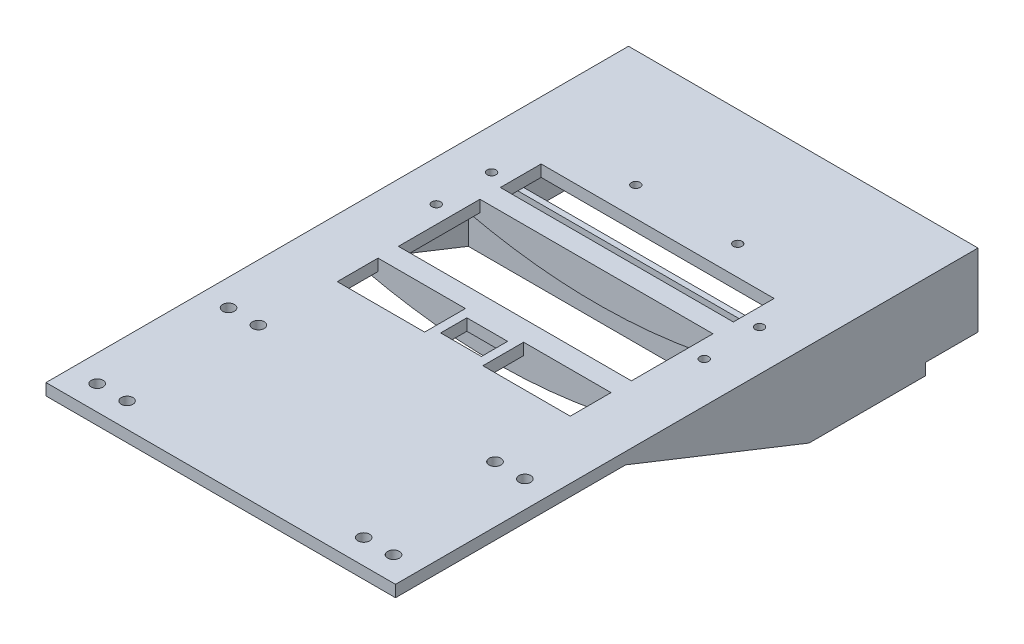
SolidWorks part; units mm, degrees
ref_plane "Front Plane" through (0, 0, 0) normal (0, 0, 1) x (1, 0, 0)
ref_plane "Top Plane" through (0, 0, 0) normal (0, 1, 0) x (1, 0, 0)
ref_plane "Right Plane" through (0, 0, 0) normal (1, 0, 0) x (0, 0, -1)
sketch "Sketch1" plane through (0, 0, 0) normal (0, 1, 0) x (1, 0, 0)
  line L0 (0, 0) -> (0, 199.1037) construction
  line L1 (-60, -40) -> (60, -40)
  line L2 (-60, -40) -> (-60, 40)
  line L3 (-40, 40) -> (40, 40)
  line L4 (60, -40) -> (60, 40)
  line L5 (-60, -40) -> (0, 0) construction
  line L6 (-60, 40) -> (60, -40) construction
  line L7 (17.5, 120) -> (-17.5, 120) construction
  line L8 (-60, 40) -> (-60, 160)
  line L9 (-40, 110) -> (40, 110)
  line L10 (60, 160) -> (60, 40)
  line L11 (-40, 40) -> (-40, 110)
  line L12 (40, 40) -> (40, 110)
  line L13 (-60, 160) -> (60, 160)
  circle A0 centre (-17.5, 120) radius 1.5
  circle A1 centre (17.5, 120) radius 1.5
  circle A2 centre (-50.87, -31.55) radius 2.025
  circle A3 centre (-40.62, -31.55) radius 2.01
  circle A4 centre (-50.87, 13.55) radius 2.025
  circle A5 centre (-40.62, 13.55) radius 2.025
  circle A6 centre (40.62, 13.55) radius 2.025
  circle A7 centre (50.87, 13.55) radius 2.025
  circle A8 centre (50.87, -31.55) radius 2.025
  circle A9 centre (40.62, -31.55) radius 2.01
  point P0 (0, 0)
  point P11 (0, 120)
  dimension "D5" = 3
  dimension "D6" = 3
  dimension "D10" = 10
  dimension "D12" = 4.05
  dimension "D13" = 8.45
  dimension "D14" = 9.13
  dimension "D15" = 4.02
  dimension "D16" = 8.45
  dimension "D17" = 19.38
  dimension "D18" = 9.13
  dimension "D19" = 19.38
  dimension "D20" = 53.55
  dimension "D21" = 53.55
  dimension "D22" = 200
  dimension "D1" = 80
  dimension "D2" = 120
  dimension "D3" = 35
  dimension "D4" = 160
  dimension "D7" = 20
  dimension "D8" = 20
  dimension "D9" = 80
  dimension "D11" = 50
extrude "Boss-Extrude1" add sketch "Sketch1" along normal blind 4
sketch "Sketch2" plane through (0, 0, 0) normal (0, -1, 0) x (1, 0, 0)
  line L0 (0, -160) -> (0, -25.4341) construction
  line L1 (60, -160) -> (37, -160)
  line L2 (60, -160) -> (60, -142)
  line L3 (60, -142) -> (37, -142)
  line L4 (37, -160) -> (37, -142)
  line L5 (60, -160) -> (-60, -160) construction
  line L6 (-60, -160) -> (-60, -142)
  line L7 (-60, -142) -> (-37, -142)
  line L8 (-37, -160) -> (-37, -142)
  line L9 (-37, -160) -> (-60, -160)
  dimension "D1" = 23
  dimension "D2" = 18
extrude "Boss-Extrude2" add sketch "Sketch2" along normal blind 21
sketch "Sketch3" plane through (60, 0, 0) normal (1, 0, 0) x (0, 0, -1)
  line L1 (142, -21) -> (142, 4)
  line L2 (-40, 4) -> (160, 4) construction
  line L3 (142, 4) -> (39.0327, 4)
  line L4 (39.0327, 4) -> (39.0327, 0)
  line L5 (-40, 0) -> (142, 0) construction
  line L7 (142, -21) -> (142, -25)
  line L9 (142, -25) -> (102, -25)
  line L10 (39.0327, 0) -> (102, -25)
  dimension "D1" = 4
  dimension "D2" = 40
extrude "Boss-Extrude3" add sketch "Sketch3" against normal blind 3
mirror "Mirror1" about plane through (0, 0, 0) normal (1, 0, 0) of "Boss-Extrude3"
fillet "Fillet2" radius 5 2 edges at (-37, 0, -151) (37, 0, -151)
sketch "Sketch4" plane through (0, 4, 0) normal (0, 1, 0) x (1, 0, 0)
  line L0 (-40, 75) -> (40, 75) construction
  line L1 (-40, 110) -> (-40, 40) construction
  line L2 (40, 40) -> (40, 110) construction
  line L3 (-40, 96) -> (-40, 92.5)
  line L4 (40, 110) -> (-40, 110) construction
  line L5 (40, 92.5) -> (40, 89)
  line L6 (-40, 96) -> (40, 96)
  line L7 (40, 96) -> (40, 89)
  line L8 (40, 89) -> (-40, 89)
  line L9 (-40, 89) -> (-40, 96)
  line L10 (40, 54) -> (40, 61)
  line L11 (40, 57.5) -> (40, 61)
  line L12 (-40, 61) -> (-40, 54)
  line L13 (-40, 54) -> (-40, 57.5)
  line L14 (-40, 54) -> (40, 54)
  line L15 (40, 61) -> (-40, 61)
  line M16 (-40, 40) -> (-40, 110)
  line M18 (40, 110) -> (40, 40)
  dimension "D1" = 14
  dimension "D2" = 7
  dimension "D3" = 14
extrude "Boss-Extrude4" add sketch "Sketch4" against normal up to surface (4 mm away) contours L8 L6 M18 M16 | L15 L12 L14 L10 M18 M16 up to face at (40.62, 0, 29.54)
sketch "Sketch5" plane through (0, 0, -54) normal (0, 0, 1) x (1, 0, 0)
  line L0 (51.5501, 0) -> (-51.5501, 0)
  spline S0 degree 2 poles (51.5501, 0) (0, -14) (-51.5501, 0) knots 0 0 0 1 1 1
  point P3 (0, 0)
  dimension "D1" = 7
extrude "Boss-Extrude5" add sketch "Sketch5" against normal up to surface (35 mm away)
ref_plane "Plane1" through (0, 0, -75) normal (0, 0, 1) x (1, 0, 0)
mirror "Mirror3" about plane through (0, 0, -75) normal (0, 0, 1) of "Boss-Extrude5"
sketch "Sketch6" plane through (0, 0, 0) normal (0, 1, 0) x (1, 0, 0)
  line L4 (-40, 89) -> (-40, 61)
  line L5 (-40, 61) -> (40, 61)
  line L6 (40, 61) -> (40, 89)
  line L7 (40, 89) -> (-40, 89)
  line L8 (-40, 89) -> (-40, 61)
  line L9 (-40, 61) -> (40, 61)
  line L10 (40, 61) -> (40, 89)
  line L11 (40, 89) -> (-40, 89)
  dimension "D1" = 0
extrude "Cut-Extrude1" cut sketch "Sketch6" against normal blind 37
sketch "Sketch7" plane through (0, 4, 0) normal (0, 1, 0) x (1, 0, 0)
  line L0 (0, 0) -> (0, 179.3192) construction
  line L1 (10, 40) -> (-10, 40)
  line L2 (-40, 40) -> (40, 40) construction
  line L3 (-10, 40) -> (-10, 54)
  line L4 (-40, 54) -> (40, 54) construction
  line L5 (-10, 54) -> (10, 54)
  line L6 (10, 40) -> (10, 54)
  line L7 (7, 51.5) -> (-7, 51.5)
  line L8 (-7, 51.5) -> (-7, 42.5)
  line L9 (-7, 42.5) -> (7, 42.5)
  line L10 (7, 51.5) -> (7, 42.5)
  point P12 (0, 54)
  point P13 (0, 40)
  point P18 (0, 51.5)
  point P19 (0, 42.5)
  dimension "D1" = 20
  dimension "D2" = 14
  dimension "D3" = 2.5
  dimension "D4" = 9
extrude "Boss-Extrude6" add sketch "Sketch7" against normal up to surface (4 mm away)
sketch "Sketch8" plane through (40, 0, 0) normal (-1, 0, 0) x (0, 0, 1)
  line L0 (-89, -2.7854) -> (-89, 4) construction
  line L1 (-89, 0) -> (-61, 0)
  line L2 (-89, 0) -> (-89, -2.7854)
  line L3 (-89, -2.7854) -> (-61, -2.7854)
  line L4 (-61, 0) -> (-61, -2.7854)
  line L5 (-89, -2.7854) -> (-61, -2.7854) construction
  line L6 (-61, 4) -> (-89, 4) construction
  line L8 (-61, -2.7854) -> (-61, 4) construction
  dimension "D1" = 4
extrude "Cut-Extrude2" cut sketch "Sketch8" against normal up to vertex and the other way up to vertex
sketch "Sketch9" plane through (0, 4, 0) normal (0, 1, 0) x (1, 0, 0)
  line L0 (-40, 110) -> (-40, 96) construction
  line L1 (-40, 89) -> (-40, 61) construction
  line L2 (40, 110) -> (-40, 110) construction
  circle A0 centre (-46, 99) radius 1.5
  circle A1 centre (-46, 80) radius 1.5
  dimension "D1" = 3
  dimension "D2" = 3
  dimension "D3" = 6
  dimension "D4" = 6
  dimension "D5" = 30
  dimension "D6" = 11
extrude "Cut-Extrude3" cut sketch "Sketch9" against normal blind 40
mirror "Mirror4" about plane through (0, 0, 0) normal (1, 0, 0) of "Cut-Extrude3"
sketch "Sketch10" plane through (0, 0, 0) normal (0, -1, 0) x (1, 0, 0)
  circle A0 centre (-30.47, -12.29) radius 2.01
  circle A1 centre (-20.32, -12.29) radius 2.01
  circle A4 centre (-30.47, 31.55) radius 2.01
  circle A5 centre (-20.32, 31.55) radius 2.01
  circle A6 centre (-10.17, 31.55) radius 2.01
  circle A8 centre (10.13, 31.55) radius 2.01
  circle A9 centre (20.28, 31.55) radius 2.01
  circle A10 centre (30.43, 31.55) radius 2.01
  circle A11 centre (-30.47, 20.27) radius 2.01
  circle A12 centre (-20.32, 20.27) radius 2.01
  circle A13 centre (-10.17, 20.27) radius 2.01
  circle A15 centre (10.13, 20.27) radius 2.01
  circle A16 centre (20.28, 20.27) radius 2.01
  circle A17 centre (30.43, 20.27) radius 2.01
  circle A18 centre (-30.47, 8.99) radius 2.01
  circle A19 centre (-20.32, 8.99) radius 2.01
  circle A20 centre (-10.17, 8.99) radius 2.01
  circle A22 centre (10.13, 8.99) radius 2.01
  circle A23 centre (20.28, 8.99) radius 2.01
  circle A24 centre (30.43, 8.99) radius 2.01
  circle A25 centre (-30.47, -2.29) radius 2.01
  circle A26 centre (-20.32, -2.29) radius 2.01
  circle A27 centre (-10.17, -2.29) radius 2.01
  circle A29 centre (10.13, -2.29) radius 2.01
  circle A30 centre (20.28, -2.29) radius 2.01
  circle A31 centre (30.43, -2.29) radius 2.01
  circle A32 centre (-10.17, -12.29) radius 2.01
  circle A34 centre (10.13, -12.29) radius 2.01
  circle A35 centre (20.28, -12.29) radius 2.01
  circle A36 centre (30.43, -12.29) radius 2.01
  circle A37 centre (-30.47, -22.29) radius 2.01
  circle A38 centre (-20.32, -22.29) radius 2.01
  circle A39 centre (-10.17, -22.29) radius 2.01
  circle A41 centre (10.13, -22.29) radius 2.01
  circle A42 centre (20.28, -22.29) radius 2.01
  circle A43 centre (30.43, -22.29) radius 2.01
  circle A44 centre (-30.47, -32.29) radius 2.01
  circle A45 centre (-20.32, -32.29) radius 2.01
  circle A46 centre (-10.17, -32.29) radius 2.01
  circle A48 centre (10.13, -32.29) radius 2.01
  circle A49 centre (20.28, -32.29) radius 2.01
  circle A50 centre (30.43, -32.29) radius 2.01
  dimension "D2" = 4.02
  dimension "D1" = 4
extrude "Cut-Extrude4" cut sketch "Sketch10" against normal blind 40
sketch "Sketch11" plane through (0, 4, 0) normal (0, 1, 0) x (1, 0, 0)
  line L1 (-33.7485, 36.7107) -> (35.422, 36.7107)
  line L2 (-33.7485, 36.7107) -> (-33.7485, -36.3646)
  line L3 (-33.7485, -36.3646) -> (35.422, -36.3646)
  line L4 (35.422, 36.7107) -> (35.422, -36.3646)
extrude "Boss-Extrude7" add sketch "Sketch11" against normal blind 2
sketch "Sketch12" plane through (0, 0, 0) normal (1, 0, 0) x (0, 0, -1)
  line L2 (-40, 0) -> (39.0327, 0)
  spline S0 degree 2 poles (-40, 0) (-0.4684, -10.0015) (39.0327, 0) knots 0 0 0 1 1 1
  dimension "D1" = 5
extrude "Boss-Extrude8" add sketch "Sketch12" along normal mid plane 2
sketch "Sketch14" plane through (0, -21, 0) normal (0, -1, 0) x (1, 0, 0)
  line L0 (-60, -142) -> (-60, -160) construction
  circle A0 centre (-58, -144) radius 1
  circle A1 centre (-53.5, -144) radius 1
  circle A2 centre (-49, -144) radius 1
  circle A3 centre (-44.5, -144) radius 1
  circle A4 centre (-40, -144) radius 1
  circle A5 centre (-53.5, -148.5) radius 1
  circle A6 centre (-49, -148.5) radius 1
  circle A7 centre (-44.5, -148.5) radius 1
  circle A8 centre (-40, -148.5) radius 1
  circle A9 centre (-53.5, -153) radius 1
  circle A10 centre (-49, -153) radius 1
  circle A11 centre (-44.5, -153) radius 1
  circle A12 centre (-40, -153) radius 1
  circle A13 centre (-53.5, -157.5) radius 1
  circle A14 centre (-49, -157.5) radius 1
  circle A15 centre (-44.5, -157.5) radius 1
  circle A16 centre (-40, -157.5) radius 1
  circle A17 centre (-58, -148.5) radius 1
  circle A18 centre (-58, -153) radius 1
  circle A19 centre (-58, -157.5) radius 1
  dimension "D1" = 2
  dimension "D2" = 2
  dimension "D4" = 5
  dimension "D5" = 4
extrude "Cut-Extrude5" cut sketch "Sketch14" against normal up to surface (21 mm away)
mirror "Mirror5" about plane through (0, 0, 0) normal (1, 0, 0) of "Cut-Extrude5"
sketch "Sketch15" plane through (0, 0, 0) normal (0, -1, 0) x (1, 0, 0)
  line L0 (-22.5, -150) -> (22.5, -150) construction
  line L1 (-22.5, -145) -> (22.5, -145)
  line L2 (-22.5, -155) -> (22.5, -155)
  line L3 (32, -160) -> (-32, -160) construction
  line L4 (-22.5, -132) -> (22.5, -132) construction
  line L5 (-22.5, -127) -> (22.5, -127)
  line L6 (-22.5, -137) -> (22.5, -137)
  arc A0 (-22.5, -145) -> (-22.5, -155) centre (-22.5, -150) ccw
  arc A1 (22.5, -155) -> (22.5, -145) centre (22.5, -150) ccw
  arc A2 (-22.5, -127) -> (-22.5, -137) centre (-22.5, -132) ccw
  arc A3 (22.5, -137) -> (22.5, -127) centre (22.5, -132) ccw
  point P2 (0, -150)
  point P14 (0, -132)
  dimension "D2" = 5
  dimension "D1" = 5
  dimension "D3" = 45
  dimension "D5" = 8
  dimension "D4" = 2
extrude "Cut-Extrude6" cut sketch "Sketch15" against normal blind 2
sketch "Sketch16" plane through (0, 0, 0) normal (0, -1, 0) x (1, 0, 0)
  line L0 (-47, 20) -> (-47, -2) construction
  line L1 (-42, 20) -> (-42, -2)
  line L2 (-52, 20) -> (-52, -2)
  line L3 (-60, -39.0327) -> (-60, 40) construction
  line L4 (-60, 40) -> (-1, 40) construction
  arc A0 (-42, 20) -> (-52, 20) centre (-47, 20) ccw
  arc A1 (-52, -2) -> (-42, -2) centre (-47, -2) ccw
  point P2 (-47, 9)
  dimension "D3" = 22
  dimension "D4" = 20
  dimension "D1" = 8
  dimension "D2" = 13
extrude "Cut-Extrude7" cut sketch "Sketch16" against normal blind 2
mirror "Mirror6" about plane through (0, 0, 0) normal (1, 0, 0) of "Cut-Extrude7"
sketch "Sketch17" plane through (57, 0, 0) normal (-1, 0, 0) x (0, 0, 1)
  line L0 (-102, -25) -> (-142, -25) construction
  line L1 (-142, 0) -> (-140, 0)
  line L2 (-142, 0) -> (-142, -25)
  line L3 (-142, -25) -> (-140, -25)
  line L4 (-140, 0) -> (-140, -25)
  dimension "D1" = 2
extrude "Boss-Extrude9" add sketch "Sketch17" along normal up to next
sketch "Sketch18" plane through (57, 0, 0) normal (-1, 0, 0) x (0, 0, 1)
  line L0 (-140, 0) -> (-39.0327, 0) construction
  line L1 (-102, -25) -> (-104, -25)
  line L2 (-102, -25) -> (-102, 0)
  line L3 (-102, 0) -> (-104, 0)
  line L4 (-104, -25) -> (-104, 0)
  dimension "D1" = 2
extrude "Boss-Extrude10" add sketch "Sketch18" along normal up to next
